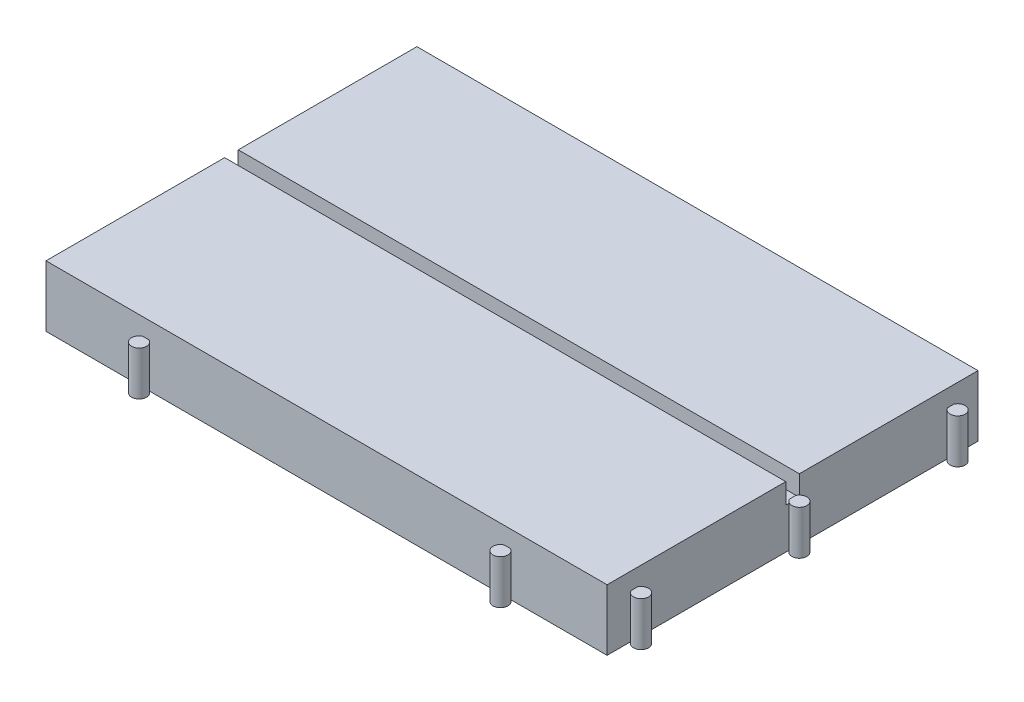
SolidWorks part; units mm, degrees
ref_plane "Front Plane" through (0, 0, 0) normal (0, 0, 1) x (1, 0, 0)
ref_plane "Top Plane" through (0, 0, 0) normal (0, 1, 0) x (1, 0, 0)
ref_plane "Right Plane" through (0, 0, 0) normal (1, 0, 0) x (0, 0, -1)
ref_plane "Plane1" through (0, 0, 0) normal (0, -1, 0) x (1, 0, 0)
sketch "Sketch1" plane through (0, 0, 0) normal (0, -1, 0) x (1, 0, 0)
  line L0 (-82.6, 0) -> (0, 0)
  line L1 (0, 0) -> (0, 26.8417)
  line L2 (0, 27.7583) -> (0, 54.6)
  line L3 (0, 54.6) -> (-82.6, 54.6)
  line L4 (-82.6, 54.6) -> (-82.6, 0)
  arc A0 (0, 26.8417) -> (0, 27.7583) centre (1, 27.3) ccw
extrude "Boss-Extrude1" add sketch "Sketch1" against normal blind 6
sketch "Sketch2" plane through (0, 6, 0) normal (0, 1, 0) x (-1, 0, 0)
  line L0 (82.6, 0) -> (0, 0)
  line L1 (0, 0) -> (0, 26.3)
  line L2 (0, 26.3) -> (82.6, 26.3)
  line L3 (82.6, 26.3) -> (82.6, 0)
extrude "Boss-Extrude2" add sketch "Sketch2" along normal blind 3
sketch "Sketch3" plane through (0, 6, 0) normal (0, 1, 0) x (-1, 0, 0)
  line L0 (0, 54.6) -> (82.6, 54.6)
  line L1 (82.6, 54.6) -> (82.6, 28.3)
  line L2 (82.6, 28.3) -> (0, 28.3)
  line L3 (0, 28.3) -> (0, 54.6)
extrude "Boss-Extrude3" add sketch "Sketch3" along normal blind 3
sketch "Sketch4" plane through (0, 6, 0) normal (0, 1, 0) x (-1, 0, 0)
  line L0 (0, 27.7583) -> (0, 26.8417)
  arc A0 (0, 26.8417) -> (0, 27.7583) centre (-1, 27.3) cw
extrude "Boss-Extrude4" add sketch "Sketch4" along normal blind 0.5
sketch "Sketch5" plane through (0, 0, 0) normal (0, -1, 0) x (1, 0, 0)
  line L0 (0, 4.4583) -> (0, 3.5417)
  arc A0 (0, 3.5417) -> (0, 4.4583) centre (1, 4) ccw
extrude "Boss-Extrude5" add sketch "Sketch5" against normal blind 6.5
sketch "Sketch6" plane through (0, 0, 0) normal (0, -1, 0) x (1, 0, 0)
  line L0 (0, 51.0583) -> (0, 50.1417)
  arc A0 (0, 50.1417) -> (0, 51.0583) centre (1, 50.6) ccw
extrude "Boss-Extrude6" add sketch "Sketch6" against normal blind 6.5
sketch "Sketch7" plane through (0, 0, 0) normal (0, -1, 0) x (1, 0, 0)
  line L0 (-68.3583, 54.6) -> (-67.4417, 54.6)
  arc A0 (-67.4417, 54.6) -> (-68.3583, 54.6) centre (-67.9, 55.6) ccw
extrude "Boss-Extrude7" add sketch "Sketch7" against normal blind 6.5
sketch "Sketch8" plane through (0, 0, 0) normal (0, -1, 0) x (1, 0, 0)
  line L0 (-15.1583, 54.6) -> (-14.2417, 54.6)
  arc A0 (-14.2417, 54.6) -> (-15.1583, 54.6) centre (-14.7, 55.6) ccw
extrude "Boss-Extrude8" add sketch "Sketch8" against normal blind 6.5
